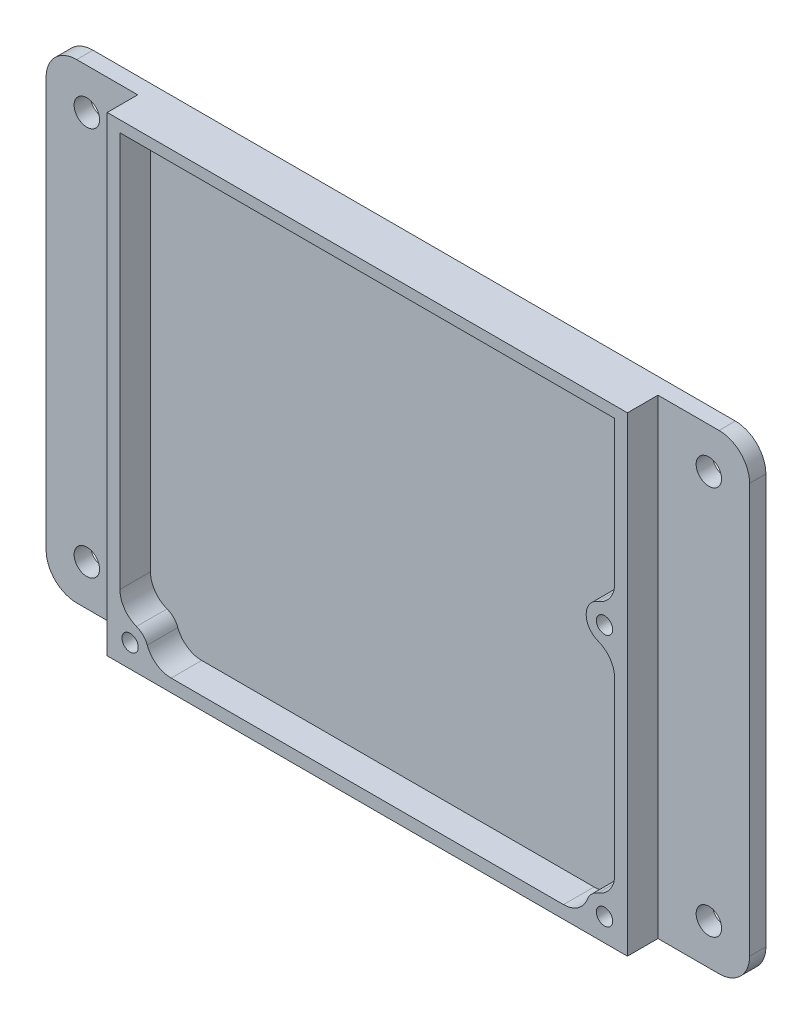
SolidWorks part; units mm, degrees
ref_plane "Front Plane" through (0, 0, 0) normal (0, 0, 1) x (1, 0, 0)
ref_plane "Top Plane" through (0, 0, 0) normal (0, 1, 0) x (1, 0, 0)
ref_plane "Right Plane" through (0, 0, 0) normal (1, 0, 0) x (0, 0, -1)
sketch "Sketch1" plane through (0, 0, 0) normal (0, 0, 1) x (1, 0, 0)
  line L1 (0, 0) -> (102.2, 0)
  line L2 (0, 0) -> (0, 92.45)
  line L3 (0, 92.45) -> (102.2, 92.45)
  line L4 (102.2, 0) -> (102.2, 92.45)
  line L5 (2.5, 2.5) -> (99.7, 2.5)
  line L6 (2.5, 2.5) -> (2.5, 90.25)
  line L7 (2.5, 90.25) -> (99.7, 90.25)
  line L8 (99.7, 2.5) -> (99.7, 90.25)
  circle A0 centre (4.5, 4.5) radius 1.6
  circle A1 centre (4.5, 4.5) radius 3.6
  circle A2 centre (97.7, 4.5) radius 1.6
  circle A3 centre (97.7, 4.5) radius 3.6
  circle A4 centre (97.7, 54.1) radius 1.6
  circle A5 centre (97.7, 54.1) radius 3.6
  dimension "D7" = 3.2
  dimension "D11" = 3.2
  dimension "D16" = 3.2
  dimension "D1" = 102.2
  dimension "D2" = 92.45
  dimension "D3" = 2.5
  dimension "D4" = 2.2
  dimension "D5" = 2.5
  dimension "D6" = 2.5
  dimension "D8" = 2
  dimension "D9" = 4.5
  dimension "D10" = 4.5
  dimension "D12" = 2
  dimension "D13" = 4.5
  dimension "D14" = 4.5
  dimension "D15" = 2
  dimension "D17" = 49.6
extrude "Boss-Extrude1" add sketch "Sketch1" along normal blind 6 contours L1 L4 L3 L2 A5 L8 A3 L5 A1 L6 L7 | L8 A5 A4 | L8 A3 L5 A2 | L5 A1 L6 A0 | L6 A1 L5 | L5 A3 L8 | L8 A5
sketch "Sketch2" plane through (0, 0, 0) normal (0, 0, -1) x (-1, 0, 0)
  line L0 (0, 92.45) -> (-102.2, 92.45) construction
  line L1 (-120.2, 0) -> (18, 0)
  line L2 (-120.2, 0) -> (-120.2, 92.45)
  line L3 (-120.2, 92.45) -> (18, 92.45)
  line L4 (18, 0) -> (18, 92.45)
  line L5 (0, 0) -> (-102.2, 0) construction
  line L7 (-51.1, 92.45) -> (-51.1, 0) construction
  circle A0 centre (-112.2, 84.45) radius 2.5
  circle A1 centre (-112.2, 8) radius 2.5
  circle A2 centre (10, 8) radius 2.5
  circle A3 centre (10, 84.45) radius 2.5
  dimension "D3" = 5
  dimension "D4" = 5
  dimension "D1" = 18
  dimension "D2" = 18
  dimension "D6" = 8
  dimension "D7" = 8
  dimension "D5" = 8
extrude "Boss-Extrude2" add sketch "Sketch2" along normal blind 3.2
fillet "Fillet1" radius 6 4 edges at (120.2, 92.45, -1.6) (120.2, 0, -1.6) (-18, 92.45, -1.6) (-18, 0, -1.6)
fillet "Fillet2" radius 5 2 edges at (99.7, 51.1067, 3) (99.7, 57.0933, 3)
fillet "Fillet3" radius 5 4 edges at (7.4933, 2.5, 3) (2.5, 7.4933, 3) (94.7067, 2.5, 3) (99.7, 7.4933, 3)
equation "\"M3HoleInner\"= 3.2mm"
equation "\"M3HoleThickness\"= 2mm"
equation "\"M3DistY\"= 49.6mm"
equation "\"M3DistX\"= 93mm"
equation "\"BoardX\"= 102.2mm"
equation "\"BoardY\" = 92.45mm"
equation "\"D1@Sketch1\"=\"BoardX\""
equation "\"D2@Sketch1\"=\"BoardY\""
equation "\"BoardThickness\"= 2.5mm"
equation "\"D3@Sketch1\"=\"BoardThickness\""
equation "\"D5@Sketch1\"=\"BoardThickness\""
equation "\"D6@Sketch1\"=\"BoardThickness\""
equation "\"D7@Sketch1\"=\"M3HoleInner\""
equation "\"D8@Sketch1\"=\"M3HoleThickness\""
equation "\"D11@Sketch1\"=\"M3HoleInner\""
equation "\"D12@Sketch1\"=\"M3HoleThickness\""
equation "\"D15@Sketch1\"=\"M3HoleThickness\""
equation "\"D16@Sketch1\"=\"M3HoleInner\""
equation "\"D17@Sketch1\"=\"M3DistY\""
equation "\"MountFlangWidth\"= 18mm"
equation "\"MountFlangHoles\"= 5.0mm"
equation "\"D1@Sketch2\"=\"MountFlangWidth\""
equation "\"D2@Sketch2\"=\"MountFlangWidth\""
equation "\"D3@Sketch2\"=\"MountFlangHoles\""
equation "\"D4@Sketch2\"=\"MountFlangHoles\""
equation "\"D7@Sketch2\"=8"
